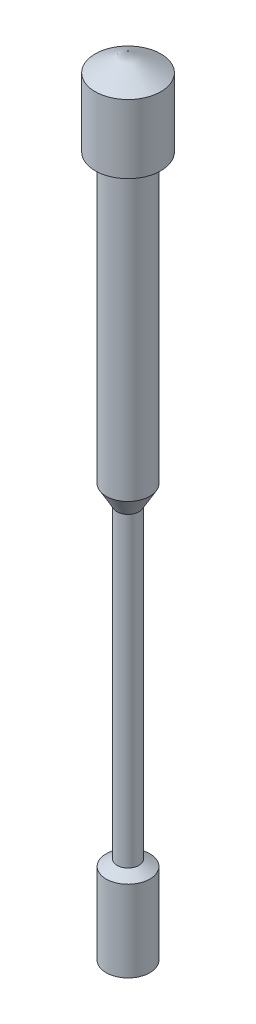
SolidWorks part; units mm, degrees
ref_plane "Front Plane" through (0, 0, 0) normal (0, 0, 1) x (1, 0, 0)
ref_plane "Top Plane" through (0, 0, 0) normal (0, 1, 0) x (1, 0, 0)
ref_plane "Right Plane" through (0, 0, 0) normal (1, 0, 0) x (0, 0, -1)
sketch "Sketch2" plane through (0, 0, 0) normal (0, 0, 1) x (1, 0, 0)
  line L0 (0, 18) -> (0.75, 17.567)
  line L1 (0.75, 17.567) -> (0.75, 16)
  line L2 (0.75, 16) -> (0.5, 16)
  line L3 (0.5, 16) -> (0.5, 9.433)
  line L4 (0.5, 9.433) -> (0.25, 9)
  line L5 (0.25, 9) -> (0.25, 2)
  line L6 (0.25, 2) -> (0.5, 1.8557)
  line L7 (0.5, 1.8557) -> (0.5, 0)
  line L8 (0.5, 0) -> (0, 0)
  line L9 (0, 0) -> (0, 0.9792) construction
  line L10 (0, 18) -> (0, 0)
  point P10 (0.5, 1.8557)
  point P13 (0.5, 1.8557)
  point P14 (0, 0)
  point P15 (0.75, 16.7835)
  point P16 (0, 0)
  dimension "D1" = 2
  dimension "D2" = 0.75
  dimension "D3" = 120
  dimension "D4" = 1
  dimension "D5" = 7
  dimension "D6" = 0.5
  dimension "D7" = 0.5
  dimension "D8" = 2
  dimension "D9" = 14
revolve "Revolve1" add sketch "Sketch2" angle 360 about L9
